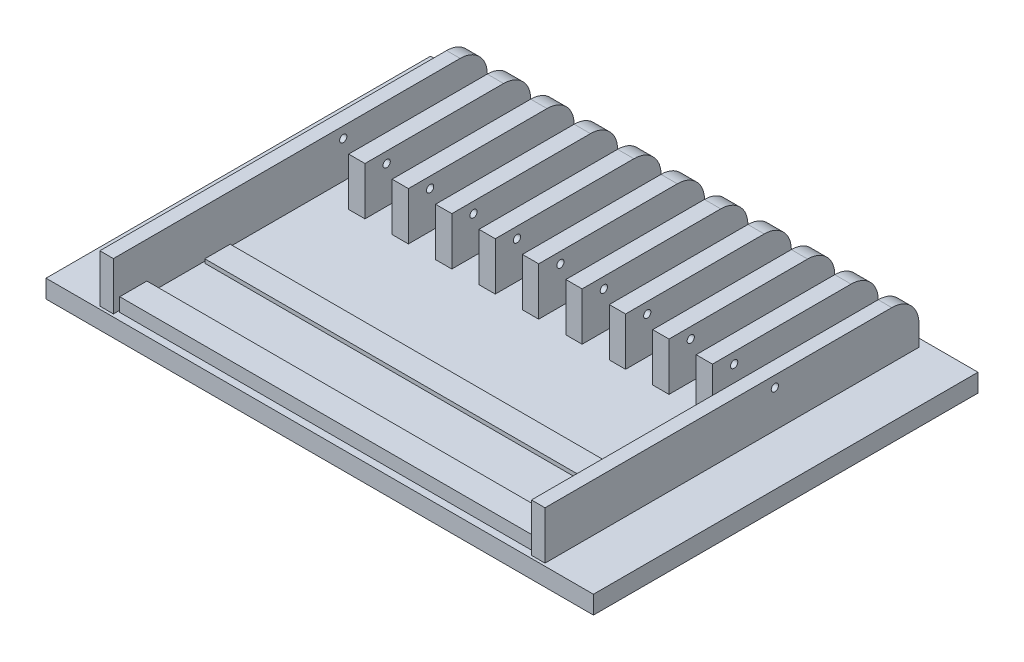
SolidWorks part; units mm, degrees
material "Maple"
ref_plane "Front Plane" through (0, 0, 0) normal (0, 0, 1) x (1, 0, 0)
ref_plane "Top Plane" through (0, 0, 0) normal (0, 1, 0) x (1, 0, 0)
ref_plane "Right Plane" through (0, 0, 0) normal (1, 0, 0) x (0, 0, -1)
sketch "Sketch1" plane through (0, 0, 0) normal (0, 1, 0) x (1, 0, 0)
  line L1 (302.5, -212.5) -> (-302.5, -212.5)
  line L2 (302.5, -212.5) -> (302.5, 212.5)
  line L3 (302.5, 212.5) -> (-302.5, 212.5)
  line L4 (-302.5, -212.5) -> (-302.5, 212.5)
  line L5 (302.5, -212.5) -> (-302.5, 212.5) construction
  line L6 (302.5, 212.5) -> (-302.5, -212.5) construction
  point P0 (0, 0)
  dimension "D1" = 605
  dimension "D2" = 425
extrude "Boss-Extrude1" add sketch "Sketch1" against normal blind 20
sketch "Sketch2" plane through (0, 0, 0) normal (1, 0, 0) x (0, 0, -1)
  line L0 (-212.5, -20) -> (-212.5, 0) construction
  line L1 (203.7, 0) -> (-209.5, 0)
  line L2 (203.7, 0) -> (203.7, 23)
  line L3 (173.7, 53) -> (-209.5, 53)
  line L4 (-209.5, 0) -> (-209.5, 53)
  line L5 (-212.5, 0) -> (212.5, 0) construction
  line L6 (212.5, -20) -> (212.5, 0) construction
  arc A0 (203.7, 23) -> (173.7, 53) centre (173.7, 23) ccw
  dimension "D1" = 30
  dimension "D2" = 53
  dimension "D3" = 3
  dimension "D4" = 8.8
extrude "Boss-Extrude2" add sketch "Sketch2" along normal mid plane 492
sketch "Sketch3" plane through (0, 0, 209.5) normal (0, 0, 1) x (1, 0, 0)
  line L0 (246, 53) -> (-246, 53) construction
  line L1 (-231, 0) -> (-201, 0)
  line L2 (-231, 0) -> (-231, 53)
  line L3 (-231, 53) -> (-201, 53)
  line L4 (-201, 0) -> (-201, 53)
  line L5 (-231, 0) -> (-201, 53) construction
  line L6 (-231, 53) -> (-201, 0) construction
  line L7 (246, 0) -> (-246, 0) construction
  line L8 (0, 0) -> (0, 53) construction
  line L9 (-183, 0) -> (-183, 53)
  line L10 (-183, 53) -> (-153, 0) construction
  line L11 (-183, 0) -> (-153, 53) construction
  line L12 (-153, 0) -> (-153, 53)
  line L13 (-183, 53) -> (-153, 53)
  line L14 (-183, 0) -> (-153, 0)
  line L15 (-135, 0) -> (-135, 53)
  line L16 (-135, 53) -> (-105, 0) construction
  line L17 (-135, 0) -> (-105, 53) construction
  line L18 (-105, 0) -> (-105, 53)
  line L19 (-135, 53) -> (-105, 53)
  line L20 (-135, 0) -> (-105, 0)
  line L21 (-87, 0) -> (-87, 53)
  line L22 (-87, 53) -> (-57, 0) construction
  line L23 (-87, 0) -> (-57, 53) construction
  line L24 (-57, 0) -> (-57, 53)
  line L25 (-87, 53) -> (-57, 53)
  line L26 (-87, 0) -> (-57, 0)
  line L27 (-39, 0) -> (-39, 53)
  line L28 (-39, 53) -> (-9, 0) construction
  line L29 (-39, 0) -> (-9, 53) construction
  line L30 (-9, 0) -> (-9, 53)
  line L31 (-39, 53) -> (-9, 53)
  line L32 (-39, 0) -> (-9, 0)
  line L33 (9, 0) -> (9, 53)
  line L34 (9, 53) -> (39, 0) construction
  line L35 (9, 0) -> (39, 53) construction
  line L36 (39, 0) -> (39, 53)
  line L37 (9, 53) -> (39, 53)
  line L38 (9, 0) -> (39, 0)
  line L39 (57, 0) -> (57, 53)
  line L40 (57, 53) -> (87, 0) construction
  line L41 (57, 0) -> (87, 53) construction
  line L42 (87, 0) -> (87, 53)
  line L43 (57, 53) -> (87, 53)
  line L44 (57, 0) -> (87, 0)
  line L45 (105, 0) -> (105, 53)
  line L46 (105, 53) -> (135, 0) construction
  line L47 (105, 0) -> (135, 53) construction
  line L48 (135, 0) -> (135, 53)
  line L49 (105, 53) -> (135, 53)
  line L50 (105, 0) -> (135, 0)
  line L51 (153, 0) -> (153, 53)
  line L52 (153, 53) -> (183, 0) construction
  line L53 (153, 0) -> (183, 53) construction
  line L54 (183, 0) -> (183, 53)
  line L55 (153, 53) -> (183, 53)
  line L56 (153, 0) -> (183, 0)
  line L57 (201, 0) -> (201, 53)
  line L58 (201, 53) -> (231, 0) construction
  line L59 (201, 0) -> (231, 53) construction
  line L60 (231, 0) -> (231, 53)
  line L61 (201, 53) -> (231, 53)
  line L62 (201, 0) -> (231, 0)
  line L63 (-216, 26.5) -> (-168, 26.5) construction
  line L64 (0, 53) -> (-9, 53) construction
  line L65 (0, 53) -> (9, 53) construction
  point P0 (-216, 26.5)
  point P12 (-168, 26.5)
  point P18 (-120, 26.5)
  point P23 (-72, 26.5)
  point P28 (-24, 26.5)
  point P33 (24, 26.5)
  point P38 (72, 26.5)
  point P43 (120, 26.5)
  point P48 (168, 26.5)
  point P53 (216, 26.5)
  dimension "D1" = 30
  dimension "D3" = 48
  dimension "D2" = 10
extrude "Cut-Extrude1" cut sketch "Sketch3" against normal through all
sketch "Sketch4" plane through (-246, 0, 0) normal (-1, 0, 0) x (0, 0, 1)
  line L0 (209.5, 0) -> (-203.7, 0) construction
  line L1 (209.5, 53) -> (209.5, 0) construction
  circle A0 centre (-44.5, 41) radius 4
  dimension "D1" = 41
  dimension "D2" = 254
  dimension "D3" = 8
extrude "Cut-Extrude2" cut sketch "Sketch4" against normal through all
sketch "Sketch5" plane through (0, 0, 0) normal (1, 0, 0) x (0, 0, -1)
  line L0 (-212.5, 0) -> (212.5, 0) construction
  line L1 (-209.5, 53) -> (20.5, 53)
  line L2 (-209.5, 53) -> (-209.5, 0)
  line L3 (-209.5, 0) -> (20.5, 0)
  line L4 (20.5, 53) -> (20.5, 0)
  dimension "D1" = 230
extrude "Cut-Extrude3" cut sketch "Sketch5" against normal mid plane 440
sketch "Sketch6" plane through (0, 0, 0) normal (0, 1, 0) x (1, 0, 0)
  line L0 (0, 0) -> (0, -212.5) construction
  line L1 (-302.5, -212.5) -> (302.5, -212.5) construction
  line L2 (-231, -209.5) -> (-246, -209.5) construction
  line L3 (229, -174.5) -> (-229, -174.5)
  line L4 (229, -174.5) -> (229, -204.5)
  line L5 (229, -204.5) -> (-229, -204.5)
  line L6 (-229, -174.5) -> (-229, -204.5)
  line L7 (229, -174.5) -> (-229, -204.5) construction
  line L8 (229, -204.5) -> (-229, -174.5) construction
  line L9 (-231, 173.7) -> (-231, -209.5) construction
  point P5 (0, -189.5)
  dimension "D1" = 5
  dimension "D2" = 30
  dimension "D3" = 2
extrude "Boss-Extrude3" add sketch "Sketch6" along normal blind 15
sketch "Sketch7" plane through (0, 0, 0) normal (0, 1, 0) x (1, 0, 0)
  line L0 (0, 0) -> (0, -174.5) construction
  line L1 (229, -174.5) -> (-229, -174.5) construction
  line L3 (-229, -82.5) -> (229, -82.5)
  line L4 (-229, -82.5) -> (-229, -110.5)
  line L5 (-229, -110.5) -> (229, -110.5)
  line L6 (229, -82.5) -> (229, -110.5)
  line L7 (-229, -82.5) -> (229, -110.5) construction
  line L8 (-229, -110.5) -> (229, -82.5) construction
  line L9 (-229, -174.5) -> (-229, -204.5) construction
  point P5 (0, -96.5)
  dimension "D1" = 28
  dimension "D2" = 92
extrude "Boss-Extrude4" add sketch "Sketch7" along normal blind 4.3
